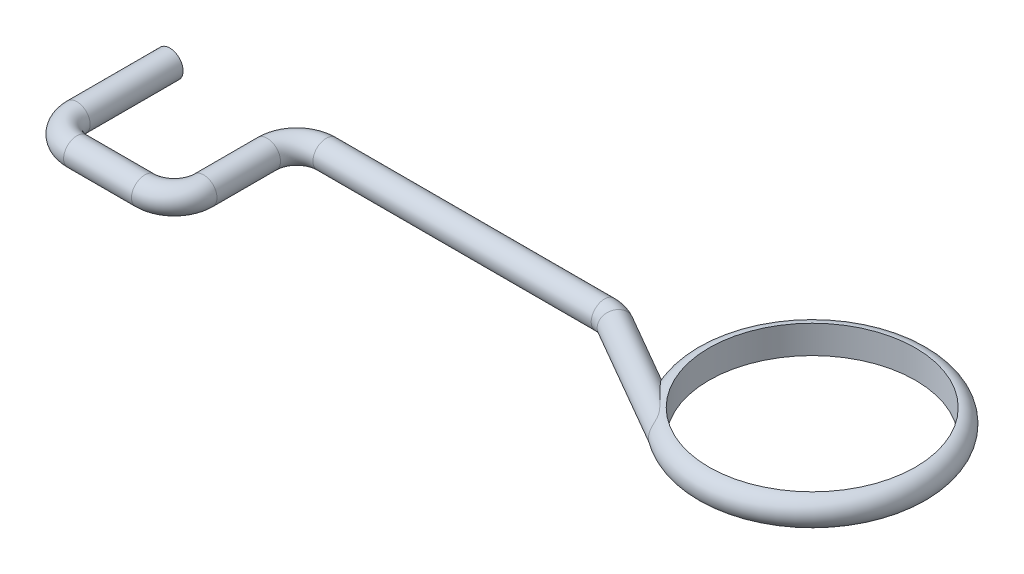
SolidWorks part; units mm, degrees
ref_plane "Front Plane" through (0, 0, 0) normal (0, 0, 1) x (1, 0, 0)
ref_plane "Top Plane" through (0, 0, 0) normal (0, 1, 0) x (1, 0, 0)
ref_plane "Right Plane" through (0, 0, 0) normal (1, 0, 0) x (0, 0, -1)
sketch "Sketch1" plane through (0, 0, 0) normal (0, 1, 0) x (1, 0, 0)
  line L0 (2.6924, 0) -> (7.4839, 0)
  line L1 (7.7379, -0.0681) -> (10.006, -1.3776)
  line L2 (0.508, -2.1082) -> (1.6764, -2.1082)
  line L3 (0, 0) -> (0, -1.6002)
  line L4 (2.1844, -1.6002) -> (2.1844, -0.508)
  arc A0 (0.508, -2.1082) -> (0, -1.6002) centre (0.508, -1.6002) cw
  arc A1 (1.6764, -2.1082) -> (2.1844, -1.6002) centre (1.6764, -1.6002) ccw
  arc A2 (2.6924, 0) -> (2.1844, -0.508) centre (2.6924, -0.508) ccw
  arc A3 (7.7379, -0.0681) -> (7.4839, 0) centre (7.4839, -0.508) ccw
  dimension "D3" = 0.508
  dimension "D4" = 0.508
  dimension "D1" = 2.1082
  dimension "D2" = 2.1844
ref_plane "Plane1" through (0, 0, 0) normal (0, 0, -1) x (-1, 0, 0)
sketch "Sketch2" plane through (0, 0, 0) normal (0, 0, -1) x (-1, 0, 0)
  circle A0 centre (0, 0) radius 0.2286
  point P0 (0, 0)
  dimension "D1" = 0.4572
sweep "Sweep1" add profiles "Sketch2" path "Sketch1"
sketch "Sketch3" plane through (0, 0, 0) normal (0, 1, 0) x (1, 0, 0)
  line L0 (10.1203, -1.1796) -> (7.8522, 0.1299) construction
  line L1 (9.8917, -1.5755) -> (10.1203, -1.1796) construction
  line L2 (9.8917, -1.5755) -> (10.1203, -1.1796)
  line L3 (7.6236, -0.266) -> (9.8917, -1.5755) construction
  line L4 (9.3741, -0.7488) -> (7.8522, 0.1299)
  line L5 (7.6236, -0.266) -> (9.8917, -1.5755)
  circle A0 centre (10.9041, 0.1569) radius 1.778
  point P7 (10.006, -1.3776)
  dimension "D2" = 3.556
sketch "Sketch4" plane through (0, 0, 0) normal (0, 0, -1) x (-1, 0, 0)
  line L5 (-12.6752, 0.2413) -> (-12.6752, -0.2413)
  arc A0 (-12.6752, 0.2413) -> (-12.6752, -0.2413) centre (-12.6752, 0) ccw
  dimension "D1" = 0.4826
sweep "Sweep2" add profiles "Sketch4" path "Sketch3"
sketch "Sketch5" plane through (0, 0, 0) normal (0, 1, 0) x (1, 0, 0)
  circle A0 centre (10.9041, 0.1569) radius 1.778 construction
  circle A1 centre (10.9041, 0.1569) radius 1.778
extrude "Cut-Extrude1" cut sketch "Sketch5" against normal through all and the other way through all
